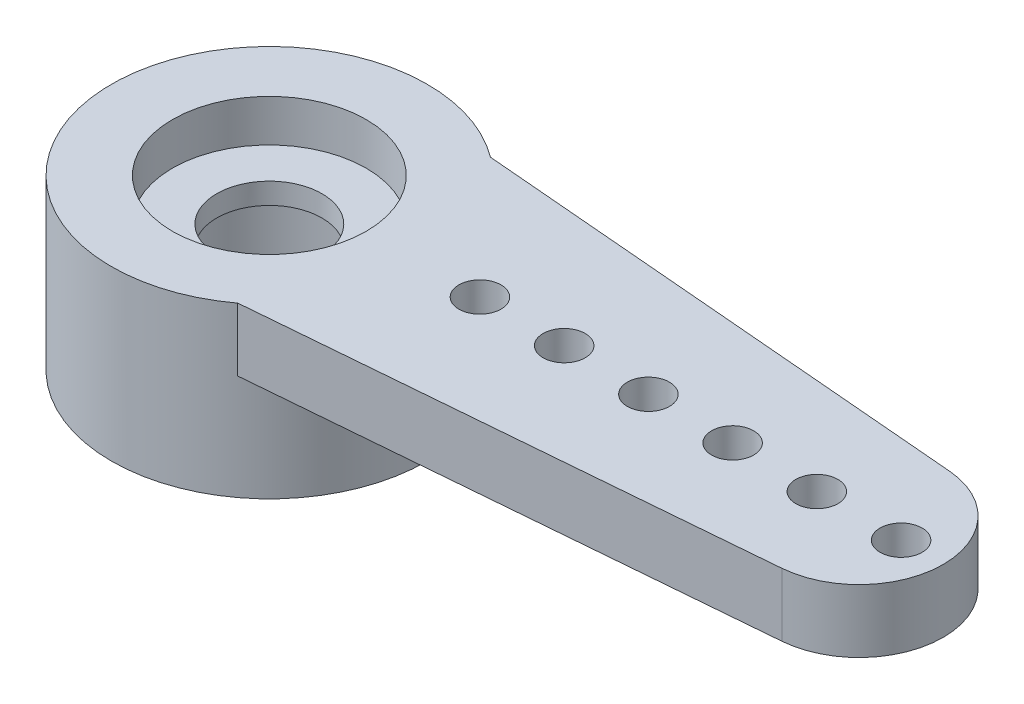
SolidWorks part; units mm, degrees
ref_plane "Front Plane" through (0, 0, 0) normal (0, 0, 1) x (1, 0, 0)
ref_plane "Top Plane" through (0, 0, 0) normal (0, 1, 0) x (1, 0, 0)
ref_plane "Right Plane" through (0, 0, 0) normal (1, 0, 0) x (0, 0, -1)
sketch "Sketch1" plane through (0, 0, 0) normal (0, 1, 0) x (1, 0, 0)
  circle A0 centre (0, 0) radius 3.75
  dimension "D1" = 7.5
extrude "Boss-Extrude1" add sketch "Sketch1" along normal blind 4
sketch "Sketch2" plane through (0, 4, 0) normal (0, 1, 0) x (1, 0, 0)
  circle A0 centre (0, 0) radius 2.3
  dimension "D1" = 4.6
extrude "Cut-Extrude1" cut sketch "Sketch2" against normal blind 1
sketch "Sketch3" plane through (0, 4, 0) normal (0, 1, 0) x (1, 0, 0)
  line L0 (16, 0) -> (-16, 0) construction
  line L3 (0, -3.75) -> (0, 3.75) construction
  line L4 (14.1684, -1.9929) -> (2.25, -3)
  line L5 (14.1684, 1.9929) -> (2.25, 3)
  circle A1 centre (0, 0) radius 3.75 construction
  arc A3 (2.25, 3) -> (2.25, -3) centre (0, 0) cw
  arc A4 (14.1684, 1.9929) -> (14.1684, -1.9929) centre (14, 0) cw
  circle A11 centre (15, 0) radius 0.5
  circle A12 centre (5, 0) radius 0.5
  circle A13 centre (7, 0) radius 0.5
  circle A14 centre (9, 0) radius 0.5
  circle A15 centre (11, 0) radius 0.5
  circle A16 centre (13, 0) radius 0.5
  point P4 (0, 0)
  dimension "D1" = 16
extrude "Boss-Extrude2" add sketch "Sketch3" against normal blind 1.5
sketch "Sketch4" plane through (0, 3, 0) normal (0, 1, 0) x (1, 0, 0)
  circle A0 centre (0, 0) radius 1.25
  dimension "D1" = 2.5
extrude "Cut-Extrude2" cut sketch "Sketch4" against normal blind 4.5
sketch "Sketch5" plane through (0, 0, 0) normal (0, -1, 0) x (1, 0, 0)
  circle A0 centre (0, 0) radius 2.3
  dimension "D1" = 4.6
extrude "Cut-Extrude3" cut sketch "Sketch5" against normal blind 2.5
